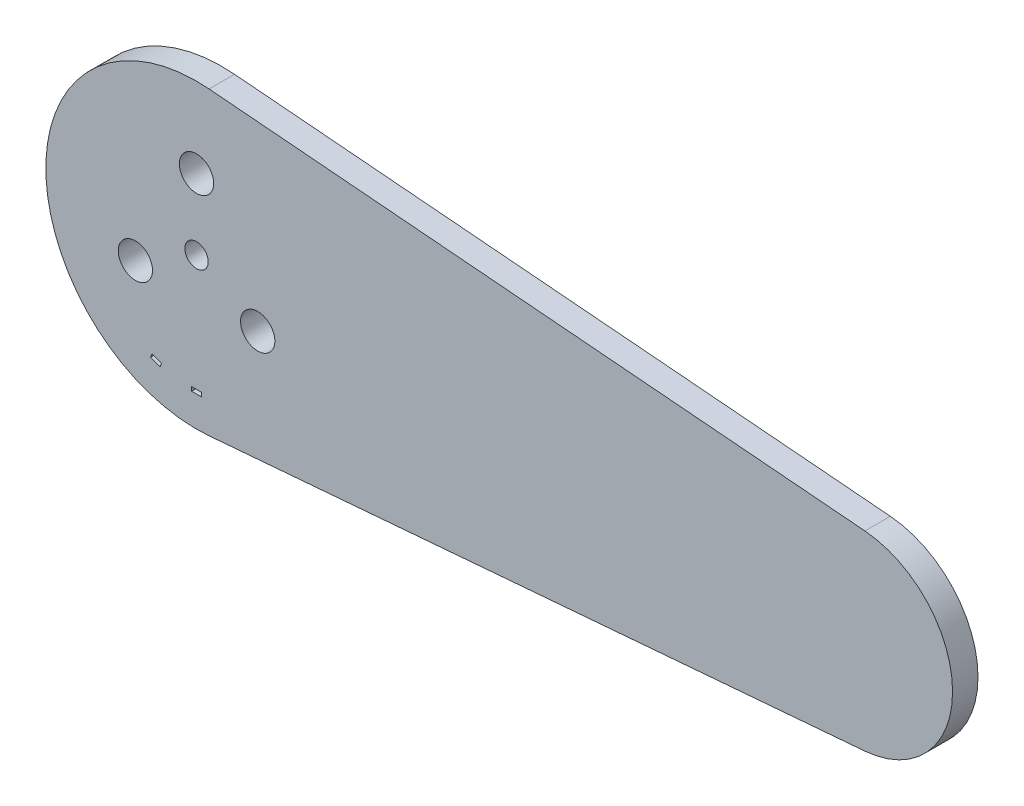
SolidWorks part; units mm, degrees
ref_plane "Front Plane" through (0, 0, 0) normal (0, 0, 1) x (1, 0, 0)
ref_plane "Top Plane" through (0, 0, 0) normal (0, 1, 0) x (1, 0, 0)
ref_plane "Right Plane" through (0, 0, 0) normal (1, 0, 0) x (0, 0, -1)
sketch "Sketch1" plane through (0, 0, 0) normal (0, 0, 1) x (1, 0, 0)
  line L84 (1.5819, 18.9078) -> (84.1319, 12.0015)
  line L85 (1.5819, -18.9078) -> (84.1319, -12.0015)
  line L86 (1.5819, 18.9078) -> (1.5819, -18.9078) construction
  line L87 (84.1319, 12.0015) -> (84.1319, -12.0015) construction
  circle A80 centre (0, 0) radius 12.7 construction
  arc A81 (1.5819, 18.9078) -> (1.5819, -18.9078) centre (0, 0) ccw
  arc A82 (84.1319, 12.0015) -> (84.1319, -12.0015) centre (83.1278, 0) cw
  circle A84 centre (0, 0) radius 1.4732
  dimension "D9" = 25.4
  dimension "D2" = 2.9464
  dimension "D10" = 37.8155
  dimension "D11" = 24.003
  dimension "D12" = 82.55
extrude "Boss-Extrude1" add sketch "Sketch1" along normal blind 3.2004
sketch "Sketch2" plane through (0, 0, 3.2004) normal (0, 0, 1) x (1, 0, 0)
  line L0 (-5.1796, -14.2308) -> (0, 0) construction
  line L1 (-4.5829, -14.448) -> (-4.4091, -13.9706)
  line L2 (-4.4091, -13.9706) -> (-5.6025, -13.5362)
  line L3 (-5.6025, -13.5362) -> (-5.7763, -14.0136)
  line L4 (-5.7763, -14.0136) -> (-4.5829, -14.448)
  line L6 (0, -15.1441) -> (0, 0) construction
  line L7 (0.635, -15.1441) -> (0.635, -14.6361)
  line L8 (0.635, -14.6361) -> (-0.635, -14.6361)
  line L9 (-0.635, -14.6361) -> (-0.635, -15.1441)
  line L10 (-0.635, -15.1441) -> (0.635, -15.1441)
  circle A1 centre (0, 0) radius 12.7 construction
  dimension "D1" = 1.27
  dimension "D2" = 0.508
  dimension "D3" = 20
  dimension "D4" = 15.1441
extrude "Cut-Extrude1" cut sketch "Sketch2" against normal up to surface (3.2004 mm away) up to face at (40.4778, 0, 0)
sketch "Sketch3" plane through (0, 0, 3.2004) normal (0, 0, 1) x (1, 0, 0)
  line L0 (0, 8.89) -> (0, 0) construction
  line L1 (0, -15.1441) -> (0, 0) construction
  circle A1 centre (0, 8.89) radius 2.159
  circle A4 centre (0, 0) radius 12.7 construction
  circle A5 centre (7.699, -4.445) radius 2.159
  circle A6 centre (-7.699, -4.445) radius 2.159
  point P13 (0, 0)
  dimension "D2" = 4.318
  dimension "D1" = 8.89
  dimension "D3" = 3
extrude "Cut-Extrude2" cut sketch "Sketch3" against normal up to surface (3.2004 mm away) up to face at (-5.0927, -13.9921, 0)
